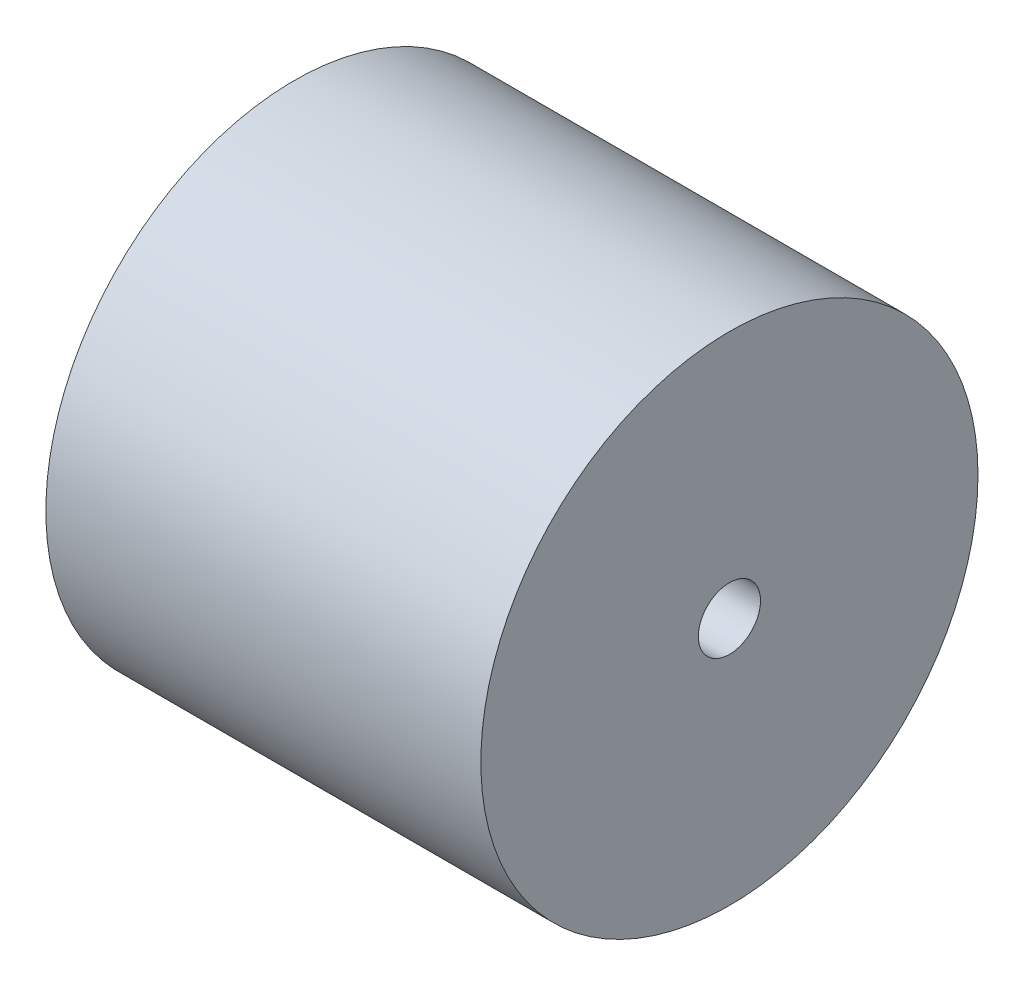
SolidWorks part; units mm, degrees
ref_plane "Front Plane" through (0, 0, 0) normal (0, 0, 1) x (1, 0, 0)
ref_plane "Top Plane" through (0, 0, 0) normal (0, 1, 0) x (1, 0, 0)
ref_plane "Right Plane" through (0, 0, 0) normal (1, 0, 0) x (0, 0, -1)
sketch "Sketch1" plane through (0, 0, 0) normal (1, 0, 0) x (0, 0, -1)
  circle A0 centre (0, 0) radius 50.8
  circle A1 centre (0, 0) radius 6.35
  dimension "D1" = 101.6
  dimension "D2" = 12.7
extrude "Boss-Extrude1" add sketch "Sketch1" along normal mid plane 88.9
